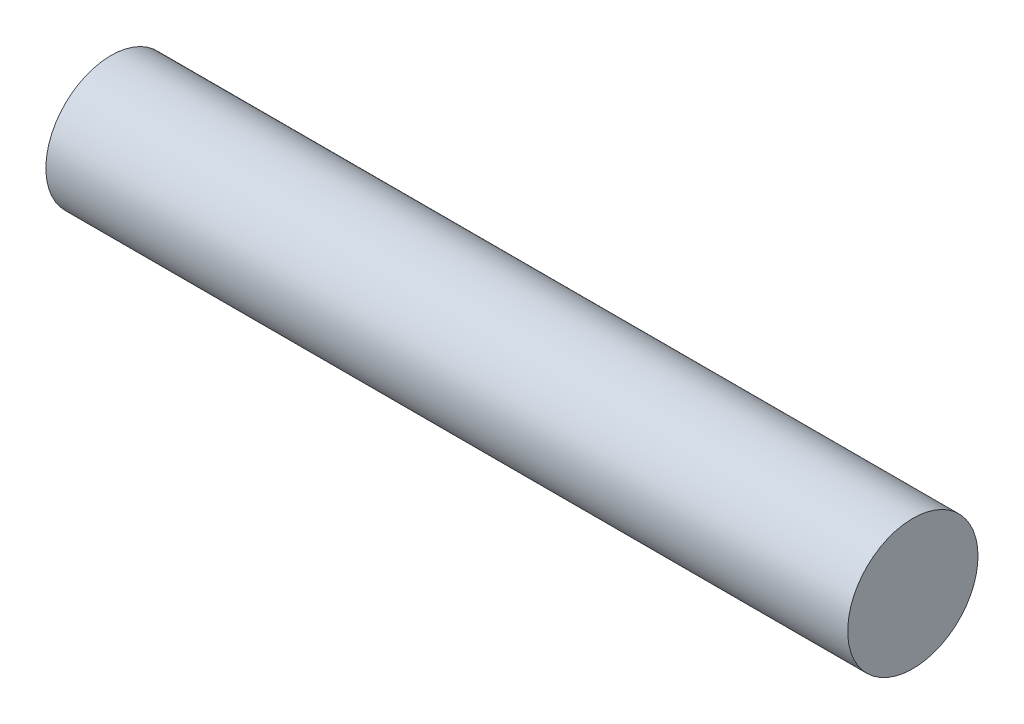
SolidWorks part; units mm, degrees
ref_plane "Front Plane" through (0, 0, 0) normal (0, 0, 1) x (1, 0, 0)
ref_plane "Top Plane" through (0, 0, 0) normal (0, 1, 0) x (1, 0, 0)
ref_plane "Right Plane" through (0, 0, 0) normal (1, 0, 0) x (0, 0, -1)
sketch "Sketch1" plane through (0, 0, 0) normal (1, 0, 0) x (0, 0, -1)
  circle A0 centre (0, 0) radius 0.65
  dimension "D1" = 1.3
extrude "Extrude1" add sketch "Sketch1" along normal blind 8
